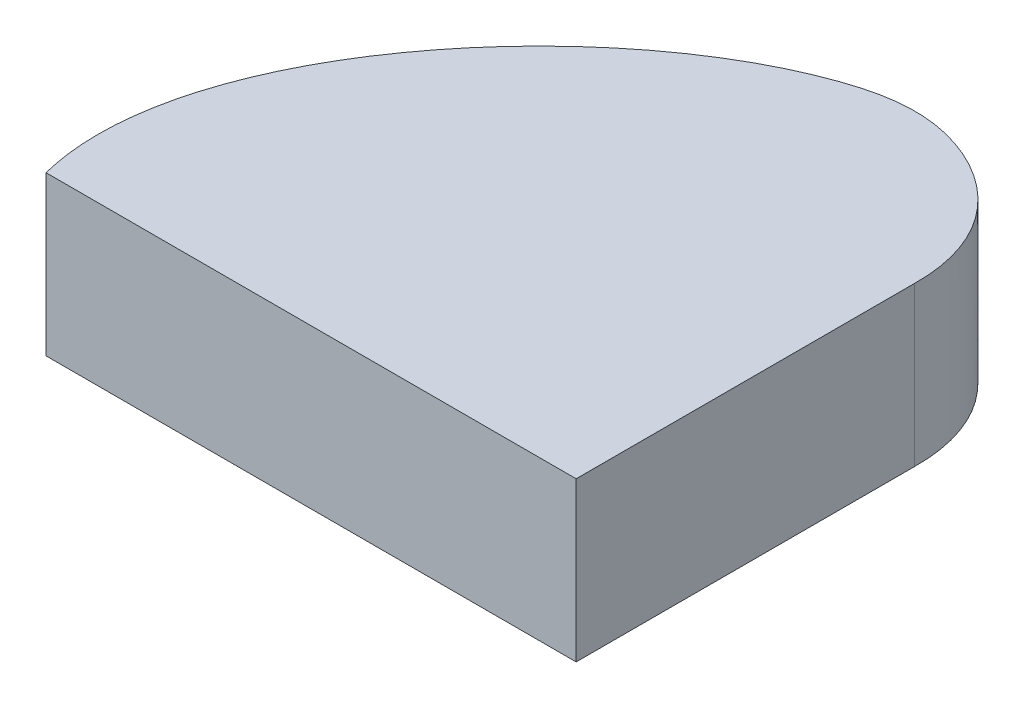
SolidWorks part; units mm, degrees
ref_plane "Front Plane" through (0, 0, 0) normal (0, 0, 1) x (1, 0, 0)
ref_plane "Top Plane" through (0, 0, 0) normal (0, 1, 0) x (1, 0, 0)
ref_plane "Right Plane" through (0, 0, 0) normal (1, 0, 0) x (0, 0, -1)
sketch "Sketch1" plane through (0, 0, 0) normal (0, 1, 0) x (1, 0, 0)
  line L1 (0, 0) -> (21.2206, 0)
  line L4 (21.2206, 0) -> (21.2206, 13.5336)
  spline S0 degree 3 poles (21.2206, 13.5336) (21.2703, 17.0998) (17.0897, 20.0714) (6.8694, 18.0689) (-1.8647, 7.3316) (0, 0) knots 0 0 0 0 0.200637 0.315853 1 1 1 1
  point P5 (0, 0)
  point P6 (11.1043, 18.1664)
  point P7 (0, 0)
  point P9 (12.4781, 19.1169)
  point P11 (4.5282, 13.2496)
  point P12 (12.6723, 19.0184)
  point P13 (16.7821, 19.32)
  point P14 (0, 0)
  point P15 (0, 0)
extrude "Boss-Extrude1" add sketch "Sketch1" along normal blind 6.35
